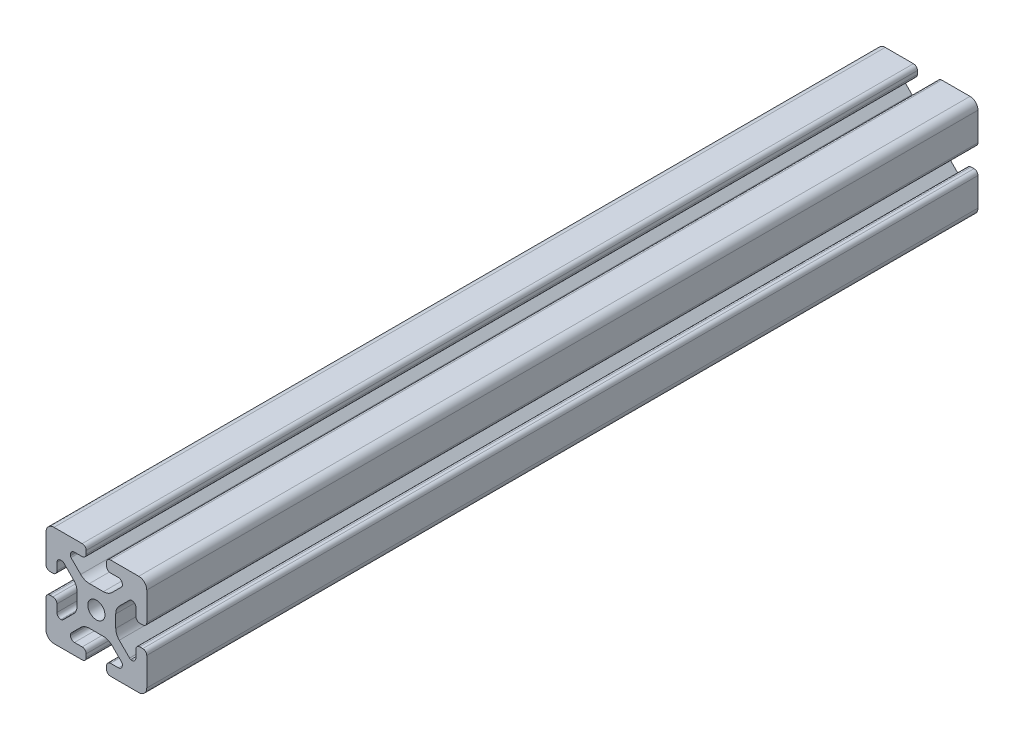
SolidWorks part; units mm, degrees
material "6105-T5 Aluminum"
ref_plane "Front Plane" through (0, 0, 0) normal (0, 0, 1) x (1, 0, 0)
ref_plane "Top Plane" through (0, 0, 0) normal (0, 1, 0) x (1, 0, 0)
ref_plane "Right Plane" through (0, 0, 0) normal (1, 0, 0) x (0, 0, -1)
sketch "Sketch1" plane through (0, 0, 0) normal (0, 0, 1) x (1, 0, 0)
  line L0 (0, 19.7407) -> (0, -19.7407) construction
  line L1 (19.0335, 0) -> (-20.7246, 0) construction
  line L2 (-8.715, -15.5246) -> (-5.63, -15.5246)
  line L3 (-10.285, -13.9546) -> (-10.285, -13.4925)
  line L4 (-6.2171, -9.1098) -> (-10.0624, -12.9551)
  line L5 (2.7773, -7.685) -> (-2.7773, -7.685)
  line L6 (10.0624, -12.9551) -> (6.2171, -9.1098)
  line L7 (10.285, -13.9546) -> (10.285, -13.4925)
  line L8 (5.63, -15.5246) -> (8.715, -15.5246)
  line L9 (4.06, -18.43) -> (4.06, -17.0946)
  line L10 (-4.06, -18.43) -> (-4.06, -17.0946)
  line L11 (15.68, -8.7154) -> (15.68, -5.63)
  line L12 (-14.11, -10.2854) -> (-13.8169, -10.2854)
  line L13 (20, -16.83) -> (20, -5.63)
  line L14 (20, 5.63) -> (20, 13.0011)
  line L15 (-16.83, 20) -> (-5.63, 20)
  line L16 (5.63, 20) -> (12.9796, 20)
  line L18 (-8.715, 15.5246) -> (-5.63, 15.5246)
  line L19 (-20, -17.0184) -> (-20, -5.7579)
  line L20 (-20, 5.573) -> (-20, 13.0045)
  line L21 (-15.68, -8.7154) -> (-15.68, -5.7579)
  line L23 (-16.6746, -20) -> (-5.63, -20)
  line L24 (5.63, -20) -> (13, -20)
  line L53 (14.11, -10.2854) -> (13.6201, -10.2854)
  line L54 (13.1637, -9.947) -> (9.0762, -5.8595)
  line L55 (7.685, -2.5008) -> (7.685, 2.5008)
  line L56 (9.0762, 5.8595) -> (13.2795, 10.0628)
  line L57 (13.8169, 10.2854) -> (14.11, 10.2854)
  line L58 (15.68, 8.7154) -> (15.68, 5.63)
  line L59 (17.25, 4.06) -> (18.43, 4.06)
  line L61 (20, 13.0011) -> (20, 16.83)
  line L62 (16.83, 20) -> (12.9796, 20)
  line L64 (4.06, 18.43) -> (4.06, 17.0946)
  line L65 (5.63, 15.5246) -> (8.715, 15.5246)
  line L66 (10.285, 13.9546) -> (10.285, 13.4925)
  line L67 (10.0624, 12.9551) -> (6.2171, 9.1098)
  line L68 (2.7773, 7.685) -> (-2.7773, 7.685)
  line L69 (-6.2171, 9.1098) -> (-10.0624, 12.9551)
  line L70 (-10.285, 13.4925) -> (-10.285, 13.9546)
  line L72 (-4.06, 17.0946) -> (-4.06, 18.43)
  line L75 (-20, 16.83) -> (-20, 13.0045)
  line L77 (-18.43, 4.003) -> (-17.25, 4.003)
  line L78 (-15.68, 5.573) -> (-15.68, 8.4757)
  line L79 (-14.0552, 10.0447) -> (-13.7199, 10.033)
  line L80 (-13.0405, 9.8238) -> (-9.0762, 5.8595)
  line L81 (-7.685, 2.5008) -> (-7.685, -2.5008)
  line L82 (-9.0762, -5.8595) -> (-13.2795, -10.0628)
  line L85 (-17.25, -4.1204) -> (-18.43, -4.1204)
  line L100 (13, -20) -> (16.83, -20)
  line L103 (18.43, -4.06) -> (17.25, -4.06)
  arc A0 (-5.63, -15.5246) -> (-4.06, -17.0946) centre (-5.63, -17.0946) cw
  arc A1 (-8.715, -15.5246) -> (-10.285, -13.9546) centre (-8.715, -13.9546) cw
  arc A2 (-10.285, -13.4925) -> (-10.0624, -12.9551) centre (-9.525, -13.4925) cw
  arc A3 (-6.2171, -9.1098) -> (-2.7773, -7.685) centre (-2.7773, -12.5496) cw
  arc A4 (2.7773, -7.685) -> (6.2171, -9.1098) centre (2.7773, -12.5496) cw
  arc A5 (10.0624, -12.9551) -> (10.285, -13.4925) centre (9.525, -13.4925) cw
  arc A6 (10.285, -13.9546) -> (8.715, -15.5246) centre (8.715, -13.9546) cw
  arc A7 (4.06, -17.0946) -> (5.63, -15.5246) centre (5.63, -17.0946) cw
  arc A8 (5.63, -20) -> (4.06, -18.43) centre (5.63, -18.43) cw
  arc A9 (-4.06, -18.43) -> (-5.63, -20) centre (-5.63, -18.43) cw
  circle A45 centre (0, 0) radius 3.4
  arc A46 (17.25, -4.06) -> (15.68, -5.63) centre (17.25, -5.63) ccw
  arc A47 (14.11, -10.2854) -> (15.68, -8.7154) centre (14.11, -8.7154) ccw
  arc A48 (13.1637, -9.947) -> (13.6201, -10.2854) centre (13.8117, -9.55) ccw
  arc A49 (7.685, -2.5008) -> (9.0762, -5.8595) centre (12.435, -2.5008) ccw
  arc A50 (9.0762, 5.8595) -> (7.685, 2.5008) centre (12.435, 2.5008) ccw
  arc A51 (13.8169, 10.2854) -> (13.2795, 10.0628) centre (13.8169, 9.5254) ccw
  arc A52 (15.68, 8.7154) -> (14.11, 10.2854) centre (14.11, 8.7154) ccw
  arc A53 (15.68, 5.63) -> (17.25, 4.06) centre (17.25, 5.63) ccw
  arc A54 (18.43, 4.06) -> (20, 5.63) centre (18.43, 5.63) ccw
  arc A55 (20, 16.83) -> (16.83, 20) centre (16.83, 16.83) ccw
  arc A56 (5.63, 20) -> (4.06, 18.43) centre (5.63, 18.43) ccw
  arc A57 (4.06, 17.0946) -> (5.63, 15.5246) centre (5.63, 17.0946) ccw
  arc A58 (10.285, 13.9546) -> (8.715, 15.5246) centre (8.715, 13.9546) ccw
  arc A59 (10.0624, 12.9551) -> (10.285, 13.4925) centre (9.525, 13.4925) ccw
  arc A60 (2.7773, 7.685) -> (6.2171, 9.1098) centre (2.7773, 12.5496) ccw
  arc A61 (-6.2171, 9.1098) -> (-2.7773, 7.685) centre (-2.7773, 12.5496) ccw
  arc A62 (-10.285, 13.4925) -> (-10.0624, 12.9551) centre (-9.525, 13.4925) ccw
  arc A63 (-8.715, 15.5246) -> (-10.285, 13.9546) centre (-8.715, 13.9546) ccw
  arc A64 (-5.63, 15.5246) -> (-4.06, 17.0946) centre (-5.63, 17.0946) ccw
  arc A65 (-4.06, 18.43) -> (-5.63, 20) centre (-5.63, 18.43) ccw
  arc A66 (-16.83, 20) -> (-20, 16.83) centre (-16.83, 16.83) ccw
  arc A67 (-20, 5.573) -> (-18.43, 4.003) centre (-18.43, 5.573) ccw
  arc A68 (-17.25, 4.003) -> (-15.68, 5.573) centre (-17.25, 5.573) ccw
  arc A69 (-14.0552, 10.0447) -> (-15.68, 8.4757) centre (-14.11, 8.4757) ccw
  arc A70 (-13.0405, 9.8238) -> (-13.7199, 10.033) centre (-13.5779, 9.2864) ccw
  arc A71 (-7.685, 2.5008) -> (-9.0762, 5.8595) centre (-12.435, 2.5008) ccw
  arc A72 (-9.0762, -5.8595) -> (-7.685, -2.5008) centre (-12.435, -2.5008) ccw
  arc A73 (-13.8169, -10.2854) -> (-13.2795, -10.0628) centre (-13.8169, -9.5254) ccw
  arc A74 (-15.68, -8.7154) -> (-14.11, -10.2854) centre (-14.11, -8.7154) ccw
  arc A75 (-15.68, -5.7579) -> (-17.25, -4.1204) centre (-17.2485, -5.6904) ccw
  arc A76 (-18.43, -4.1204) -> (-20, -5.7579) centre (-18.4315, -5.6904) ccw
  arc A77 (-20, -17.0184) -> (-16.6746, -20) centre (-16.8354, -16.8341) ccw
  arc A88 (16.83, -20) -> (20, -16.83) centre (16.83, -16.83) ccw
  arc A89 (20, -5.63) -> (18.43, -4.06) centre (18.43, -5.63) ccw
  dimension "D2" = 6.8
  dimension "D7" = 20.57
  dimension "D1" = 40
  dimension "D3" = 4.32
  dimension "D4" = 15.37
  dimension "D5" = 20
  dimension "D6" = 4.32
  dimension "D9" = 15.37
extrude "Extrude1" add sketch "Sketch1" against normal blind 330
